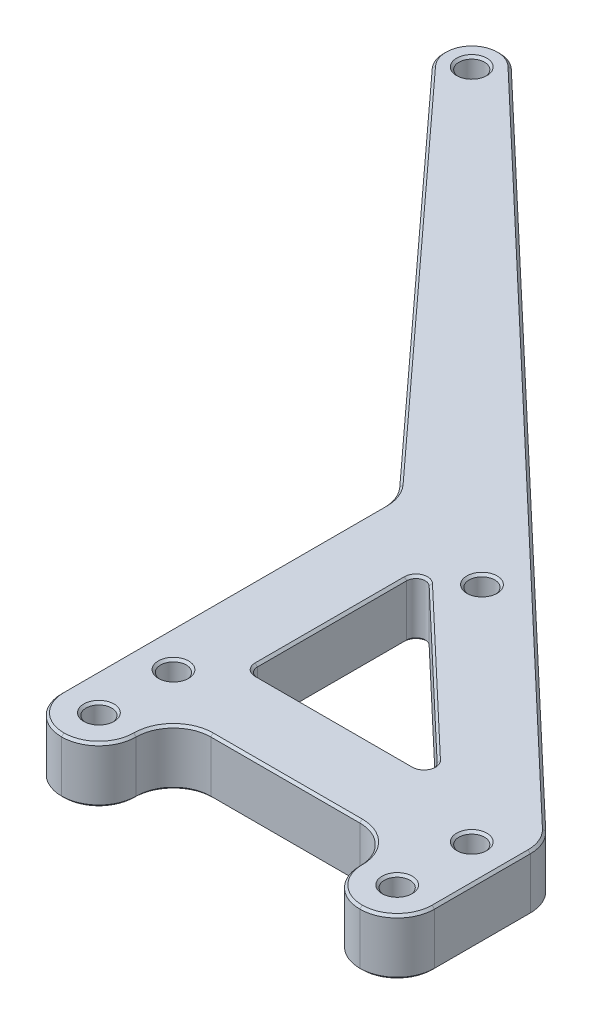
SolidWorks part; units mm, degrees
ref_plane "Front Plane" through (0, 0, 0) normal (0, 0, 1) x (1, 0, 0)
ref_plane "Top Plane" through (0, 0, 0) normal (0, 1, 0) x (1, 0, 0)
ref_plane "Right Plane" through (0, 0, 0) normal (1, 0, 0) x (0, 0, -1)
sketch "Sketch1" plane through (0, 0, 0) normal (0, 1, 0) x (1, 0, 0)
  line L6 (50.8, -6.35) -> (50.7997, -6.35)
  line L7 (-6.35, 0) -> (-6.35, 54.969)
  line L8 (-8.0135, 59.2538) -> (-67.0149, 123.7864)
  line L9 (-60.2214, 130.4543) -> (55.1715, 20.9279)
  line L10 (57.15, 16.3222) -> (57.15, 0)
  line L11 (44.45, -0.0003) -> (44.45, 0.0003)
  line L12 (38.1003, 6.35) -> (12.6997, 6.35)
  line L13 (6.35, 0.0003) -> (6.35, -0.0003)
  line L14 (0.0003, -6.35) -> (0, -6.35)
  line L15 (35.8166, 21.7889) -> (9.0304, 47.2133)
  line L16 (6.35, 46.0619) -> (6.35, 20.6375)
  line L17 (7.9375, 19.05) -> (34.7237, 19.05)
  circle A0 centre (0, 0) radius 2.1828
  circle A3 centre (50.8, 12.7) radius 2.1828
  circle A4 centre (-63.5, 127) radius 2.1828
  arc A11 (-60.2214, 130.4543) -> (-67.0149, 123.7864) centre (-63.5, 127) ccw
  arc A12 (50.8, -6.35) -> (57.15, 0) centre (50.8, 0) ccw
  arc A13 (0, -6.35) -> (-6.35, 0) centre (0, 0) cw
  arc A14 (55.1715, 20.9279) -> (57.15, 16.3222) centre (50.8, 16.3222) cw
  arc A15 (-6.35, 54.969) -> (-8.0135, 59.2538) centre (-12.7, 54.969) ccw
  circle A16 centre (0, 12.7) radius 2.1828
  circle A17 centre (50.8, 0) radius 2.1828
  arc A18 (12.6997, 6.35) -> (6.35, 0.0003) centre (12.6997, 0.0003) ccw
  arc A19 (44.45, 0.0003) -> (38.1003, 6.35) centre (38.1003, 0.0003) ccw
  arc A20 (6.35, -0.0003) -> (0.0003, -6.35) centre (0.0003, -0.0003) cw
  arc A21 (44.45, -0.0003) -> (50.7997, -6.35) centre (50.7997, -0.0003) ccw
  arc A22 (35.8166, 21.7889) -> (34.7237, 19.05) centre (34.7237, 20.6375) cw
  arc A23 (6.35, 20.6375) -> (7.9375, 19.05) centre (7.9375, 20.6375) ccw
  arc A24 (9.0304, 47.2133) -> (6.35, 46.0619) centre (7.9375, 46.0619) ccw
  circle A32 centre (13.7279, 51.5096) radius 2.1828
  point P16 (57.15, -6.35)
  point P19 (-6.35, -6.35)
  point P22 (57.15, 19.05)
  point P25 (-6.35, 57.4343)
  point P37 (44.45, 6.35)
  point P40 (6.35, -6.35)
  point P43 (44.45, -6.35)
  point P53 (0, 0)
  dimension "D5" = 4.3656
  dimension "D6" = 9.525
  dimension "D7" = 6.35
  dimension "D8" = 4.3656
  dimension "D11" = 4.3656
  dimension "D12" = 15.875
  dimension "D20" = 12.7
  dimension "D21" = 6.3497
  dimension "D15" = 6.35
  dimension "D16" = 4.3656
  dimension "D17" = 4.3656
  dimension "D25" = 1.5875
  dimension "D26" = 4.3656
  dimension "D2" = 6.35
  dimension "D3" = 50.8
  dimension "D4" = 12.7
  dimension "D9" = 127
  dimension "D10" = 63.5
  dimension "D13" = 25.4
  dimension "D14" = 63.5
  dimension "D18" = 12.7
  dimension "D19" = 12.7
  dimension "D22" = 12.7
  dimension "D23" = 12.7
  dimension "D24" = 12.7
  dimension "D31" = 6.35
  dimension "D32" = 107.9952
extrude "Boss-Extrude1" add sketch "Sketch1" along normal blind 9.525
chamfer "Chamfer1" distance 0.3969 angle 45 60 edges at (7.3109, 9.525, -47.5205) (6.35, 9.525, -33.3497) (6.815, 9.525, -19.515) (21.3306, 9.525, -19.05) (36.1982, 9.525, -20.0492) (22.4235, 9.525, -34.5011) (50.8, 9.525, 2.1828) (-63.5, 9.525, -124.8172) (0, 9.525, 2.1828) (50.7999, 9.525, 6.35) (46.3098, 9.525, 4.4902) (44.45, 9.525, 0) (42.5902, 9.525, -4.4902) (25.4, 9.525, -6.35) (8.2098, 9.525, -4.4902) (6.35, 9.525, 0) (4.4902, 9.525, 4.4902) (0.0001, 9.525, 6.35) (-4.4901, 9.525, 4.4901) (-6.35, 9.525, -27.4845) (-6.7805, 9.525, -57.2672) (-37.5142, 9.525, -91.5201) (-66.836, 9.525, -130.3989) (-2.5249, 9.525, -75.6911) (56.6345, 9.525, -18.8285) (57.15, 9.525, -8.1611) (55.2901, 9.525, 4.4901) (50.8, 9.525, -10.5172) (0, 9.525, -10.5172) (21.3306, 0, -19.05) (6.815, 0, -19.515) (6.35, 0, -33.3497) (7.3109, 0, -47.5205) (22.4235, 0, -34.5011) (36.1982, 0, -20.0492) (57.15, 0, -8.1611) (56.6345, 0, -18.8285) (-2.5249, 0, -75.6911) (-66.836, 0, -130.3989) (-37.5142, 0, -91.5201) (-6.7805, 0, -57.2672) (-6.35, 0, -27.4845) (-4.4901, 0, 4.4901) (0.0001, 0, 6.35) (4.4902, 0, 4.4902) (6.35, 0, 0) (8.2098, 0, -4.4902) (25.4, 0, -6.35) (42.5902, 0, -4.4902) (44.45, 0, 0) (46.3098, 0, 4.4902) (50.7999, 0, 6.35) (55.2901, 0, 4.4901) (-63.5, 0, -124.8172) (0, 0, 2.1828) (50.8, 0, -10.5172) (0, 0, -10.5172) (50.8, 0, 2.1828) (13.7279, 9.525, -49.3268) (13.7279, 0, -49.3268)
